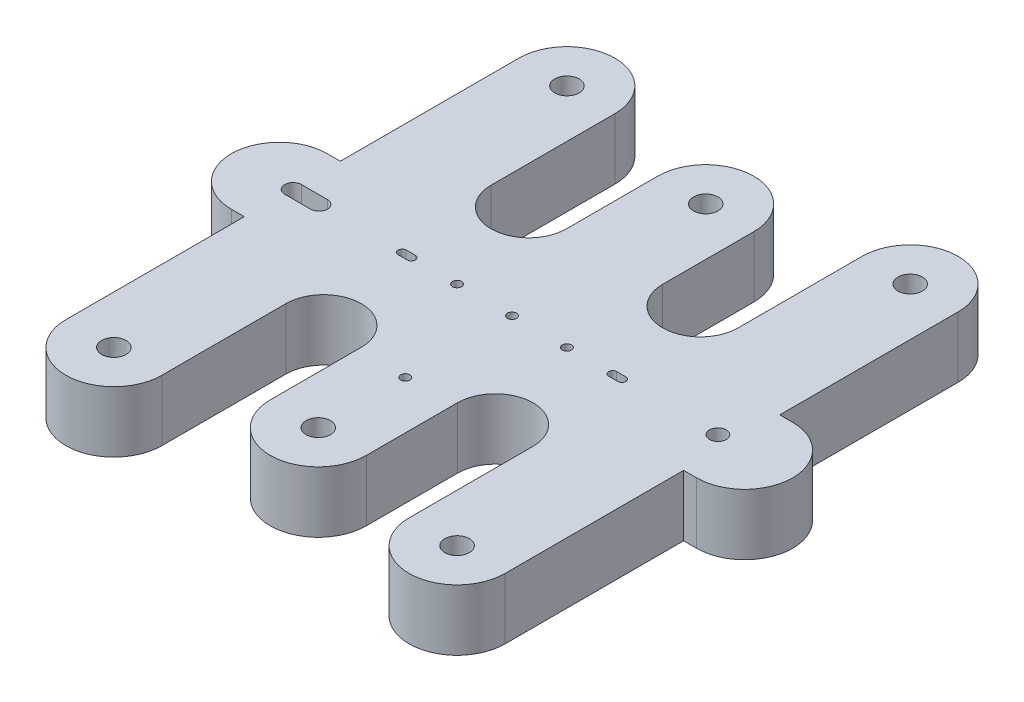
SolidWorks part; units mm, degrees
material "Ceramic Porcelain"
ref_plane "Front Plane" through (0, 0, 0) normal (0, 0, 1) x (1, 0, 0)
ref_plane "Top Plane" through (0, 0, 0) normal (0, 1, 0) x (1, 0, 0)
ref_plane "Right Plane" through (0, 0, 0) normal (1, 0, 0) x (0, 0, -1)
sketch "Sketch1" plane through (0, 0, 0) normal (0, 1, 0) x (1, 0, 0)
  line L0 (-14.4, 14.85) -> (-14.4, 3.15)
  line L1 (14.4, -14.85) -> (14.4, -3.15)
  line L2 (0, -55) -> (0, 55) construction
  line L3 (-55, 0) -> (55, 0) construction
  line L4 (-8.1, 14.85) -> (-8.1, 6.725)
  line L5 (8.1, 6.725) -> (8.1, 14.85)
  line L6 (-3.15, 12.7) -> (-3.15, 6.725)
  line L7 (14.4, -3.15) -> (15.25, -3.15)
  line L8 (3.15, 12.7) -> (3.15, 6.725)
  line L9 (-8.1, -6.725) -> (-8.1, -14.85)
  line L11 (-3.15, -12.7) -> (-3.15, -6.725)
  line L12 (8.1, -14.85) -> (8.1, -6.725)
  line L13 (3.15, -12.7) -> (3.15, -6.725)
  line L14 (-15.25, 3.15) -> (-14.4, 3.15)
  line L15 (14.4, 3.15) -> (15.25, 3.15)
  line L16 (-15.25, -3.15) -> (-14.4, -3.15)
  line L18 (-14.4, -3.15) -> (-14.4, -14.85)
  line L19 (14.4, 3.15) -> (14.4, 14.85)
  circle A0 centre (-11.25, 14.85) radius 0.8
  circle A1 centre (0, 12.7) radius 0.8
  circle A2 centre (11.25, 14.85) radius 0.8
  circle A3 centre (11.25, -14.85) radius 0.8
  circle A4 centre (0, -12.7) radius 0.8
  circle A5 centre (-11.25, -14.85) radius 0.8
  arc A6 (-8.1, 14.85) -> (-14.4, 14.85) centre (-11.25, 14.85) ccw
  arc A7 (3.15, 12.7) -> (-3.15, 12.7) centre (0, 12.7) ccw
  arc A8 (14.4, 14.85) -> (8.1, 14.85) centre (11.25, 14.85) ccw
  arc A9 (8.1, -14.85) -> (14.4, -14.85) centre (11.25, -14.85) ccw
  arc A10 (-3.15, -12.7) -> (3.15, -12.7) centre (0, -12.7) ccw
  arc A11 (-14.4, -14.85) -> (-8.1, -14.85) centre (-11.25, -14.85) ccw
  arc A12 (-3.15, 6.725) -> (-8.1, 6.725) centre (-5.625, 6.725) cw
  arc A13 (3.15, 6.725) -> (8.1, 6.725) centre (5.625, 6.725) ccw
  arc A14 (8.1, -6.725) -> (3.15, -6.725) centre (5.625, -6.725) ccw
  arc A15 (-3.15, -6.725) -> (-8.1, -6.725) centre (-5.625, -6.725) ccw
  arc A16 (-15.25, 3.15) -> (-15.25, -3.15) centre (-15.25, 0) ccw
  arc A17 (15.25, -3.15) -> (15.25, 3.15) centre (15.25, 0) ccw
  dimension "D3" = 30.5
  dimension "D1" = 12.7
  dimension "D2" = 6.3
  dimension "D12" = 1.6
  dimension "D4" = 29.7
  dimension "D5" = 14.85
  dimension "D6" = 22.5
  dimension "D7" = 11.25
  dimension "D8" = 15.25
  dimension "D9" = 25.4
  dimension "D10" = 13.45
  dimension "D11" = 6.725
extrude "Extrude9" add sketch "Sketch1" along normal blind 4
sketch "Sketch2" plane through (0, 0, 0) normal (0, 1, 0) x (1, 0, 0)
  line L0 (-14.35, 0) -> (-12.65, 0) construction
  line L1 (-2.2, 0) -> (2.2, 0) construction
  line L2 (-14.35, 0.55) -> (-12.65, 0.55)
  line L3 (-14.35, -0.55) -> (-12.65, -0.55)
  line L4 (0, -2.2) -> (0, 2.2) construction
  arc A0 (-14.35, 0.55) -> (-14.35, -0.55) centre (-14.35, 0) ccw
  arc A1 (-12.65, -0.55) -> (-12.65, 0.55) centre (-12.65, 0) ccw
  circle A2 centre (13.5, 0) radius 0.55
  point P5 (-13.5, 0)
  dimension "D2" = 1.1
  dimension "D1" = 1.1
  dimension "D3" = 13.5
  dimension "D4" = 1.7
  dimension "D5" = 13.5
extrude "Extrude10" cut sketch "Sketch2" along normal through all
sketch "Sketch3" plane through (0, 0, 0) normal (0, 1, 0) x (1, 0, 0)
  line L0 (-7.2, 0) -> (-6.6, 0) construction
  line L1 (-2.2, 0) -> (2.2, 0) construction
  line L2 (-7.2, 0.2644) -> (-6.6, 0.2644)
  line L3 (-7.2, -0.2644) -> (-6.6, -0.2644)
  line L4 (6.6, 0) -> (7.2, 0) construction
  line L5 (6.6, 0.2644) -> (7.2, 0.2644)
  line L6 (6.6, -0.2644) -> (7.2, -0.2644)
  line L7 (0, -2.2) -> (0, 2.2) construction
  arc A0 (-7.2, 0.2644) -> (-7.2, -0.2644) centre (-7.2, 0) ccw
  arc A1 (-6.6, -0.2644) -> (-6.6, 0.2644) centre (-6.6, 0) ccw
  arc A2 (6.6, 0.2644) -> (6.6, -0.2644) centre (6.6, 0) ccw
  arc A3 (7.2, -0.2644) -> (7.2, 0.2644) centre (7.2, 0) ccw
  circle A4 centre (-3.6, 0) radius 0.3
  circle A5 centre (3.6, 0) radius 0.3
  circle A6 centre (0, 0) radius 0.3
  circle A7 centre (0, -7) radius 0.3
  point P5 (-6.9, 0)
  point P10 (6.9, 0)
  dimension "D2" = 0.6
  dimension "D1" = 0.6
  dimension "D3" = 14.4
  dimension "D4" = 7.2
  dimension "D5" = 3
  dimension "D6" = 3
  dimension "D7" = 7
extrude "Extrude11" cut sketch "Sketch3" along normal blind 10
